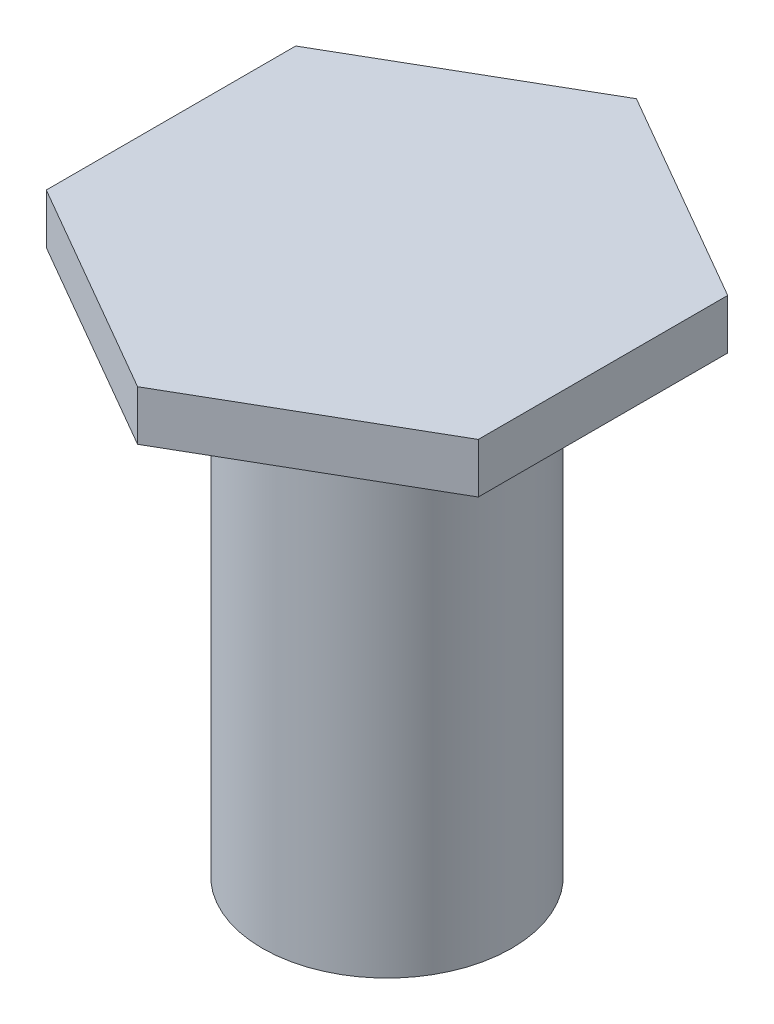
SolidWorks part; units mm, degrees
ref_plane "Front Plane" through (0, 0, 0) normal (0, 0, 1) x (1, 0, 0)
ref_plane "Top Plane" through (0, 0, 0) normal (0, 1, 0) x (1, 0, 0)
ref_plane "Right Plane" through (0, 0, 0) normal (1, 0, 0) x (0, 0, -1)
sketch "Sketch1" plane through (0, 0, 0) normal (0, 1, 0) x (1, 0, 0)
  circle A0 centre (0, 0) radius 5
extrude "Boss-Extrude1" add sketch "Sketch1" along normal blind 20
ref_plane "Plane1" through (0, 20, 0) normal (0, 1, 0) x (1, 0, 0)
sketch "Sketch2" plane through (0, 20, 0) normal (0, 1, 0) x (1, 0, 0)
  circle A0 centre (0, 0) radius 10
extrude "Boss-Extrude2" add sketch "Sketch2" along normal blind 2
ref_plane "Plane2" through (0, 22, 0) normal (0, 1, 0) x (1, 0, 0)
sketch "Sketch3" plane through (0, 22, 0) normal (0, 1, 0) x (1, 0, 0)
  line L1 (0, 10) -> (8.6603, 5)
  line L3 (8.6603, 5) -> (8.6603, -5)
  line L4 (8.6603, -5) -> (0, -10)
  line L5 (0, -10) -> (-8.6603, -5)
  line L6 (-8.6603, -5) -> (-8.6603, 5)
  line L7 (-8.6603, 5) -> (0, 10)
  circle A0 centre (0, 0) radius 10 construction
  point P19 (0, 0)
  dimension "D1" = 6
extrude "Cut-Extrude1" cut sketch "Sketch3" against normal blind 2 flip side to cut
